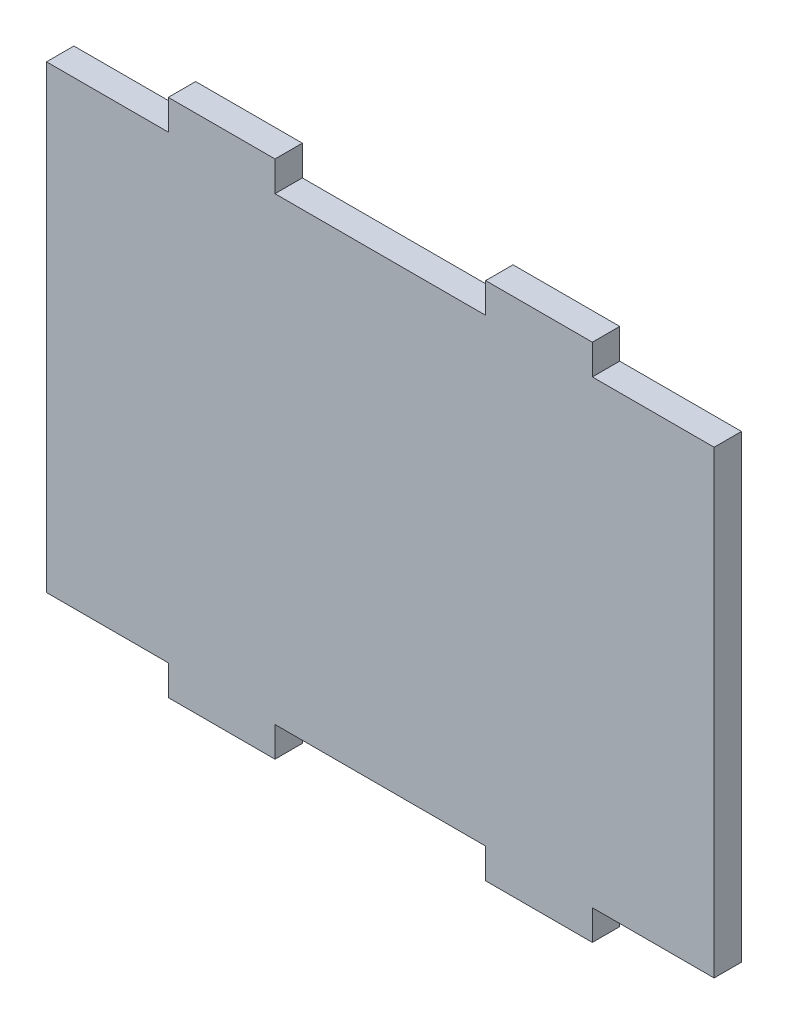
SolidWorks part; units mm, degrees
ref_plane "Plan de face" through (0, 0, 0) normal (0, 0, 1) x (1, 0, 0)
ref_plane "Plan de dessus" through (0, 0, 0) normal (0, 1, 0) x (1, 0, 0)
ref_plane "Plan de droite" through (0, 0, 0) normal (1, 0, 0) x (0, 0, -1)
sketch "Sketch1" plane through (0, 0, 0) normal (0, 0, 1) x (1, 0, 0)
  line L0 (0, -45.1875) -> (0, 57.9375) construction
  line L1 (-75.5712, 0) -> (73.3038, 0) construction
  line L2 (-61, -42) -> (-61, 42)
  line L3 (-61, -42) -> (-38.75, -42)
  line L4 (-38.75, -42) -> (-38.75, -47.5)
  line L5 (-38.75, -47.5) -> (-19.25, -47.5)
  line L6 (-19.25, -47.5) -> (-19.25, -42)
  line L7 (-19.25, -42) -> (19.25, -42)
  line L8 (-19.25, 42) -> (19.25, 42)
  line L9 (-19.25, 47.5) -> (-19.25, 42)
  line L10 (-38.75, 47.5) -> (-19.25, 47.5)
  line L11 (-38.75, 42) -> (-38.75, 47.5)
  line L12 (-61, 42) -> (-38.75, 42)
  line L13 (61, 42) -> (38.75, 42)
  line L14 (38.75, 42) -> (38.75, 47.5)
  line L15 (38.75, 47.5) -> (19.25, 47.5)
  line L16 (19.25, 47.5) -> (19.25, 42)
  line L17 (19.25, -47.5) -> (19.25, -42)
  line L18 (38.75, -47.5) -> (19.25, -47.5)
  line L19 (38.75, -42) -> (38.75, -47.5)
  line L20 (61, -42) -> (38.75, -42)
  line L21 (61, -42) -> (61, 42)
  point P4 (0, 0)
  point P8 (61, 0)
  point P19 (-61, 0)
  point P25 (0, 42)
  point P26 (0, -42)
  dimension "D1" = 19.5
  dimension "D2" = 19.25
  dimension "D3" = 5.5
  dimension "D4" = 122
  dimension "D5" = 84
extrude "Boss-Extrude1" add sketch "Sketch1" along normal blind 5
